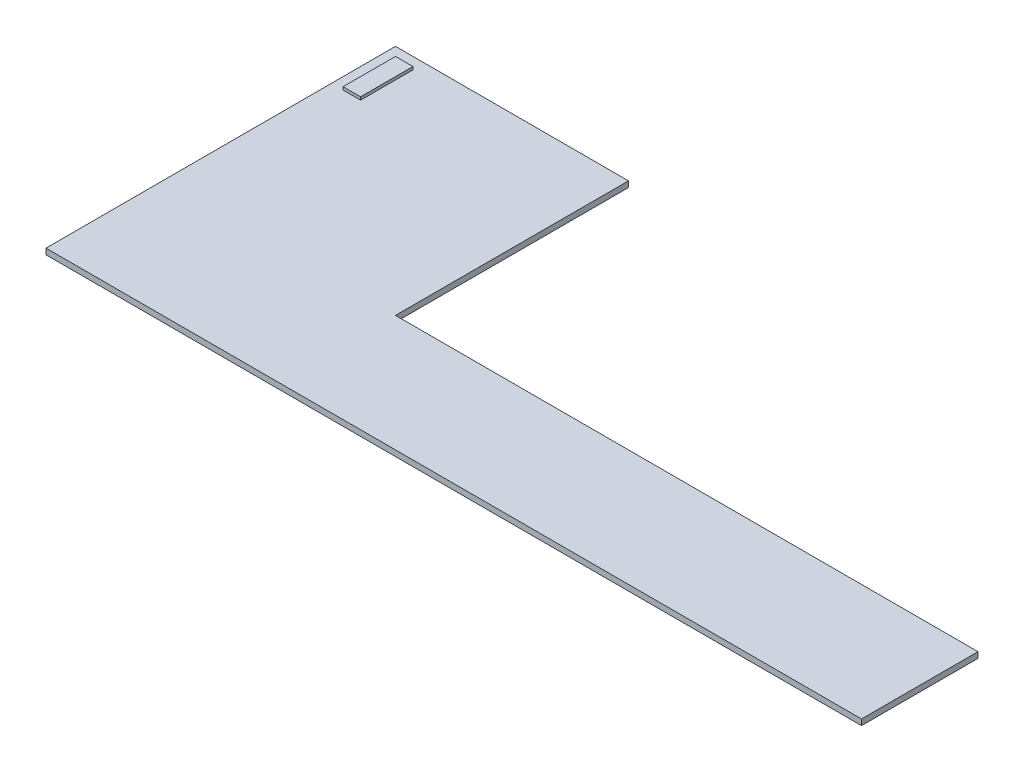
SolidWorks part; units mm, degrees
ref_plane "Front Plane" through (0, 0, 0) normal (0, 0, 1) x (1, 0, 0)
ref_plane "Top Plane" through (0, 0, 0) normal (0, 1, 0) x (1, 0, 0)
ref_plane "Right Plane" through (0, 0, 0) normal (1, 0, 0) x (0, 0, -1)
sketch "Sketch1" plane through (0, 0, 0) normal (0, 1, 0) x (1, 0, 0)
  line L0 (0, 0) -> (0, 101.6)
  line L1 (0, 0) -> (254, 0)
  line L2 (254, 0) -> (254, -50.8)
  line L3 (254, -50.8) -> (-101.6, -50.8)
  line L4 (-101.6, -50.8) -> (-101.6, 101.6)
  line L5 (-101.6, 101.6) -> (0, 101.6)
  dimension "D5" = 152.4
  dimension "D1" = 101.6
  dimension "D2" = 254
  dimension "D3" = 50.8
  dimension "D4" = 355.6
extrude "Boss-Extrude1" add sketch "Sketch1" along normal blind 2.54
sketch "Sketch2" plane through (0, 2.54, 0) normal (0, 1, 0) x (1, 0, 0)
  line L0 (0, 101.6) -> (-101.6, 101.6) construction
  line L1 (-96.52, 96.52) -> (-88.9, 96.52)
  line L2 (-96.52, 96.52) -> (-96.52, 88.9)
  line L3 (-96.52, 88.9) -> (-88.9, 88.9)
  line L4 (-88.9, 96.52) -> (-88.9, 88.9)
  line L5 (-96.52, 88.9) -> (-88.9, 88.9)
  line L6 (-96.52, 88.9) -> (-96.52, 96.52)
  line L7 (-96.52, 96.52) -> (-88.9, 96.52)
  line L8 (-88.9, 88.9) -> (-88.9, 96.52)
  line L9 (-96.52, 96.52) -> (-88.9, 96.52)
  line L10 (-96.52, 96.52) -> (-96.52, 88.9)
  line L11 (-96.52, 88.9) -> (-88.9, 88.9)
  line L12 (-88.9, 96.52) -> (-88.9, 88.9)
  line L13 (-101.6, 101.6) -> (-101.6, -50.8) construction
  line L15 (-96.52, 88.9) -> (-88.9, 88.9)
  line L16 (-96.52, 88.9) -> (-96.52, 81.28)
  line L17 (-96.52, 81.28) -> (-88.9, 81.28)
  line L18 (-88.9, 88.9) -> (-88.9, 81.28)
  line L19 (-96.52, 81.28) -> (-88.9, 81.28)
  line L20 (-96.52, 81.28) -> (-96.52, 73.66)
  line L21 (-96.52, 73.66) -> (-88.9, 73.66)
  line L22 (-88.9, 81.28) -> (-88.9, 73.66)
  dimension "D1" = 7.62
  dimension "D2" = 7.62
  dimension "D3" = 5.08
  dimension "D4" = 5.08
  dimension "D5" = 7.62
extrude "Boss-Extrude2" add sketch "Sketch2" along normal blind 1.27 contours L4 L1 L2 L3 | L18 L3 L16 L17 | L22 L17 L20 L21
